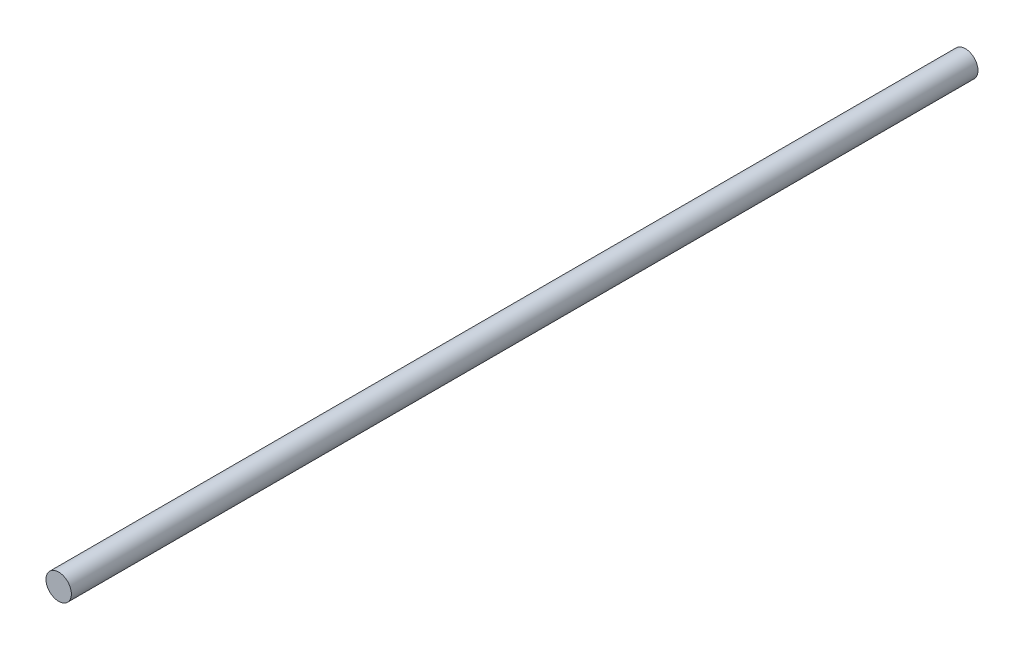
SolidWorks part; units mm, degrees
ref_plane "Front Plane" through (0, 0, 0) normal (0, 0, 1) x (1, 0, 0)
ref_plane "Top Plane" through (0, 0, 0) normal (0, 1, 0) x (1, 0, 0)
ref_plane "Right Plane" through (0, 0, 0) normal (1, 0, 0) x (0, 0, -1)
sketch "Sketch1" plane through (0, 0, 0) normal (0, 0, 1) x (1, 0, 0)
  circle A0 centre (0, 0) radius 3.5
  dimension "D1" = 7
extrude "Boss-Extrude1" add sketch "Sketch1" along normal blind 250
